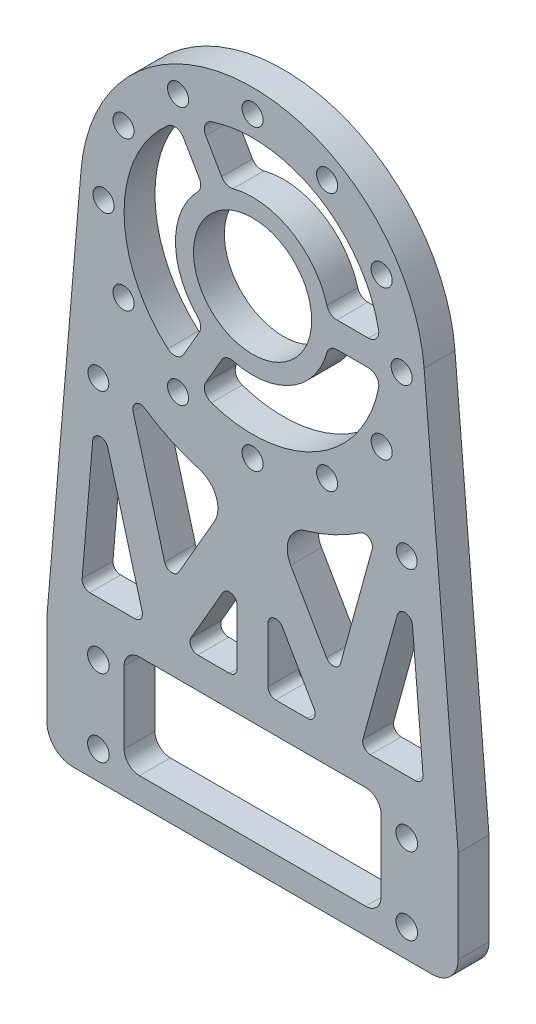
SolidWorks part; units mm, degrees
material "Thornel Mat VMA"
ref_plane "前视基准面" through (0, 0, 0) normal (0, 0, 1) x (1, 0, 0)
ref_plane "上视基准面" through (0, 0, 0) normal (0, 1, 0) x (1, 0, 0)
ref_plane "右视基准面" through (0, 0, 0) normal (1, 0, 0) x (0, 0, -1)
sketch "草图1" plane through (0, 0, 0) normal (0, 0, 1) x (1, 0, 0)
  line L0 (-40, 10) -> (-33.381, 88.3211)
  line L1 (-40, 10) -> (40, 10)
  line L2 (-40, 10) -> (-40, -10)
  line L3 (-40, -10) -> (40, -10)
  line L4 (40, 10) -> (40, -10)
  line L5 (-40, 10) -> (40, -10) construction
  line L6 (-40, -10) -> (40, 10) construction
  line L7 (-30, 7.5) -> (30, 7.5) construction
  line L8 (-30, 7.5) -> (-30, -7.5) construction
  line L9 (-30, -7.5) -> (30, -7.5) construction
  line L10 (30, 7.5) -> (30, -7.5) construction
  line L11 (-30, 7.5) -> (30, -7.5) construction
  line L12 (-30, -7.5) -> (30, 7.5) construction
  line L13 (33.381, 88.3211) -> (40, 10)
  circle A0 centre (0, 85.5) radius 33.5
  circle A1 centre (-30, -7.5) radius 2.1
  circle A2 centre (30, -7.5) radius 2.1
  circle A3 centre (30, 7.5) radius 2.1
  circle A4 centre (-30, 7.5) radius 2.1
  circle A5 centre (0, 85.5) radius 25
  point P0 (0, 0)
  point P6 (0, 0)
  dimension "D4" = 67
  dimension "D6" = 4.2
  dimension "D9" = 50
  dimension "D1" = 60
  dimension "D2" = 15
  dimension "D3" = 80
  dimension "D5" = 93
  dimension "D7" = 2
  dimension "D8" = 2
extrude "凸台-拉伸1" add sketch "草图1" along normal blind 6 contours A0 A5 | A0 L0 L1 L13 | L4 L1 L2 L3 A4 A3 A2 A1
sketch "草图3" plane through (0, 0, 6) normal (0, 0, 1) x (1, 0, 0)
  circle A0 centre (0, 85.5) radius 29 construction
  circle A1 centre (0, 114.5) radius 2.05
  circle A2 centre (14.5, 110.6147) radius 2.05
  circle A3 centre (25.1147, 100) radius 2.05
  circle A4 centre (29, 85.5) radius 2.05
  circle A5 centre (25.1147, 71) radius 2.05
  circle A6 centre (14.5, 60.3853) radius 2.05
  circle A7 centre (0, 56.5) radius 2.05
  circle A8 centre (-14.5, 60.3853) radius 2.05
  circle A9 centre (-25.1147, 71) radius 2.05
  circle A10 centre (-29, 85.5) radius 2.05
  circle A11 centre (-25.1147, 100) radius 2.05
  circle A12 centre (-14.5, 110.6147) radius 2.05
  point P29 (0, 85.5)
  dimension "D1" = 58
  dimension "D2" = 4.1
  dimension "D3" = 12
extrude "切除-拉伸1" cut sketch "草图3" against normal through all
sketch "草图4" plane through (0, 0, 6) normal (0, 0, 1) x (1, 0, 0)
  line L1 (-14.6024, 105.7921) -> (-7.7775, 93.9711)
  line L2 (-10.2723, 108.2921) -> (-3.4474, 96.4711)
  line L5 (24.8747, 83) -> (11.225, 83)
  line L6 (24.8747, 88) -> (11.225, 88)
  line L7 (-14.6024, 65.2079) -> (-7.7775, 77.0289)
  line L8 (-10.2723, 62.7079) -> (-3.4474, 74.5289)
  circle A0 centre (0, 85.5) radius 11.5
  arc A1 (-9.5602, 97.0587) -> (-9.5602, 73.9413) centre (0, 85.5) ccw
  circle A2 centre (0, 85.5) radius 25
  arc A3 (14.7902, 88) -> (-5.23, 99.5587) centre (0, 85.5) ccw
  arc A4 (-5.23, 71.4413) -> (14.7902, 83) centre (0, 85.5) ccw
  point P24 (0, 85.5)
  circle M13 centre (0, 85.5) radius 25
  dimension "D1" = 23
  dimension "D2" = 50
  dimension "D6" = 30
  dimension "D3" = 5
  dimension "D5" = 3
extrude "凸台-拉伸2" add sketch "草图4" against normal up to surface (6 mm away) separate body contours A0 L2 L1 M13 | A0 L5 L6 M13 | A0 L7 L8 M13 | L1 A1 L7 A0 | L8 A4 L5 A0 | L6 A3 L2 A0 up to face at (-23.0647, 71, 0)
combine bodies "组合1" operation type add bodies to combine 108 107
fillet "圆角1" radius 2 12 edges at (14.7902, 88, 3) (-5.23, 99.5587, 3) (24.8747, 88, 3) (-5.23, 71.4413, 3) (14.7902, 83, 3) (24.8747, 83, 3) (-10.2723, 62.7079, 3) (-10.2723, 108.2921, 3) (-9.5602, 73.9413, 3) (-14.6024, 65.2079, 3) (-9.5602, 97.0587, 3) (-14.6024, 105.7921, 3)
sketch "草图5" plane through (0, 0, 6) normal (0, 0, 1) x (1, 0, 0)
  line L1 (-40, -10) -> (40, -10)
  line L2 (-40, -10) -> (-40, -13)
  line L3 (-40, -13) -> (40, -13)
  line L4 (40, -10) -> (40, -13)
  dimension "D1" = 3
extrude "凸台-拉伸3" add sketch "草图5" against normal up to surface (6 mm away) up to face at (7.1078, 73.189, 0)
fillet "圆角2" radius 5 2 edges at (40, -13, 3) (-40, -13, 3)
sketch "草图6" plane through (0, 0, 0) normal (0, 0, -1) x (-1, 0, 0)
  line L0 (-39.3239, 18) -> (39.3239, 18)
  line L1 (-30, 7.5) -> (30, 7.5) construction
  line L2 (-30, 7.5) -> (-30, -7.5) construction
  line L3 (-30, -7.5) -> (30, -7.5) construction
  line L4 (30, 7.5) -> (30, -7.5) construction
  line L5 (-25, 12) -> (25, 12)
  line L6 (-25, 12) -> (-25, -8)
  line L7 (-25, -8) -> (25, -8)
  line L8 (25, 12) -> (25, -8)
  line L9 (-25, 12) -> (25, -8) construction
  line L10 (-25, -8) -> (25, 12) construction
  line L11 (-33.381, 88.3211) -> (-40, 10) construction
  line L12 (40, 10) -> (33.381, 88.3211) construction
  line L13 (16.1676, 26.9969) -> (26.1749, 63.3404)
  line L14 (0, 55) -> (16.1676, 26.9969)
  line L15 (34.0213, 9.4947) -> (27.4023, 87.8158)
  line L16 (34.0213, 9.4947) -> (27.4023, 87.8158)
  line L17 (0, 48) -> (-17.3205, 18)
  line L18 (-27.4023, 87.8158) -> (-34.0213, 9.4947)
  line L19 (-27.4023, 87.8158) -> (-34.0213, 9.4947)
  line L20 (0, 48) -> (17.3205, 18)
  line L21 (17.3205, 18) -> (29.5493, 62.4113)
  line L22 (-17.3205, 18) -> (-29.5493, 62.4113)
  line L23 (0, 55) -> (-16.1676, 26.9969)
  line L24 (-16.1676, 26.9969) -> (-26.1749, 63.3404)
  line L25 (19.2986, 12) -> (32.9237, 61.4821)
  line L26 (0, 41) -> (16.7432, 12)
  line L27 (0, 41) -> (-16.7432, 12)
  line L28 (18.4734, 9.0031) -> (32.9237, 61.4821) construction
  line L29 (0, 41) -> (18.4734, 9.0031) construction
  line L30 (0, 41) -> (-18.4734, 9.0031) construction
  line L31 (-19.2986, 12) -> (-32.9237, 61.4821)
  line L32 (-18.4734, 9.0031) -> (-32.9237, 61.4821) construction
  line L33 (0, 41) -> (0, 18)
  line L34 (-3, 41) -> (-3, 18)
  line L35 (3, 41) -> (3, 18)
  circle A0 centre (0, 85.5) radius 37.5
  point P4 (0, 2)
  dimension "D3" = 75
  dimension "D1" = 20
  dimension "D2" = 50
  dimension "D4" = 6
  dimension "D7" = 60
  dimension "D8" = 60
  dimension "D13" = 2
  dimension "D14" = 25
  dimension "D5" = 6
  dimension "D6" = 6
  dimension "D9" = 3.5
  dimension "D10" = 3.5
  dimension "D11" = 3
  dimension "D12" = 3
extrude "切除-拉伸2" cut sketch "草图6" against normal blind 10 contours L8 L5 L6 L7 | L0 L31 L19 | A0 L24 L23 | A0 L14 L13 | L25 L0 L16 | L34 L27 L0 | L26 L35 L0
fillet "圆角3" radius 3 4 edges at (25, -8, 3) (-25, 12, 3) (-25, -8, 3) (25, 12, 3)
fillet "圆角4" radius 1.5 16 edges at (-3, 18, 3) (-3, 35.8038, 3) (-13.2791, 18, 3) (13.2791, 18, 3) (3, 35.8038, 3) (3, 18, 3) (-16.1676, 26.9969, 3) (-24.4466, 57.0639, 3) (-33.3025, 18, 3) (-20.9508, 18, 3) (-30.4018, 52.3234, 3) (16.1676, 26.9969, 3) (24.4466, 57.0639, 3) (30.4018, 52.3234, 3) (20.9508, 18, 3) (33.3025, 18, 3)
fillet "圆角5" radius 5 2 edges at (3.9227, 48.2057, 3) (-3.9227, 48.2057, 3)
sketch "草图7" plane through (0, 0, 0) normal (0, 0, -1) x (-1, 0, 0)
  line L0 (-30, 55) -> (30, 55) construction
  line L1 (0, 55) -> (0, 0) construction
  circle A0 centre (-30, 55) radius 2.025
  circle A1 centre (30, 55) radius 2.025
  dimension "D1" = 4.05
  dimension "D2" = 55
  dimension "D3" = 60
extrude "切除-拉伸3" cut sketch "草图7" against normal blind 10
